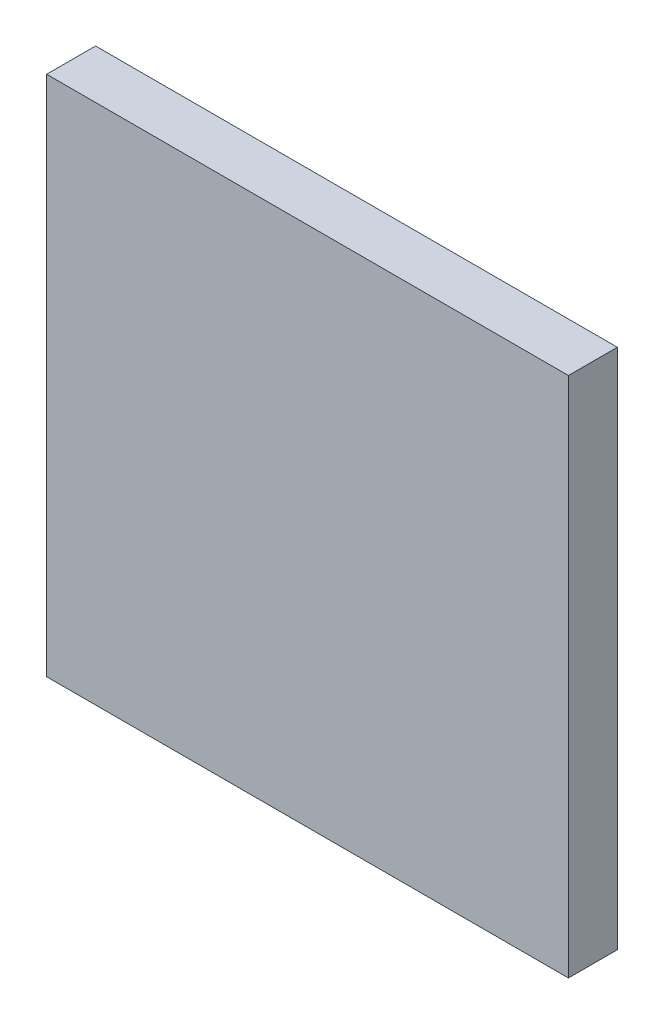
SolidWorks part; units mm, degrees
ref_plane "Front Plane" through (0, 0, 0) normal (0, 0, 1) x (1, 0, 0)
ref_plane "Top Plane" through (0, 0, 0) normal (0, 1, 0) x (1, 0, 0)
ref_plane "Right Plane" through (0, 0, 0) normal (1, 0, 0) x (0, 0, -1)
sketch "Sketch1" plane through (0, 0, 0) normal (0, 0, 1) x (1, 0, 0)
  line L2 (0, 0) -> (40, 0)
  line L3 (0, 0) -> (0, 40)
  line L4 (0, 40) -> (40, 40)
  line L5 (40, 0) -> (40, 40)
  dimension "D1" = 40
  dimension "D2" = 40
extrude "Boss-Extrude1" add sketch "Sketch1" along normal blind 3.75
sketch "Sketch2" plane through (0, 0, 3.75) normal (0, 0, 1) x (1, 0, 0)
  line L0 (0, 0) -> (40, 40) construction
  point P4 (20, 20)
sketch "Sketch3" plane through (0, 0, 0) normal (0, 0, -1) x (-1, 0, 0)
  circle A0 centre (-20, 20) radius 10 construction
  dimension "D1" = 20
